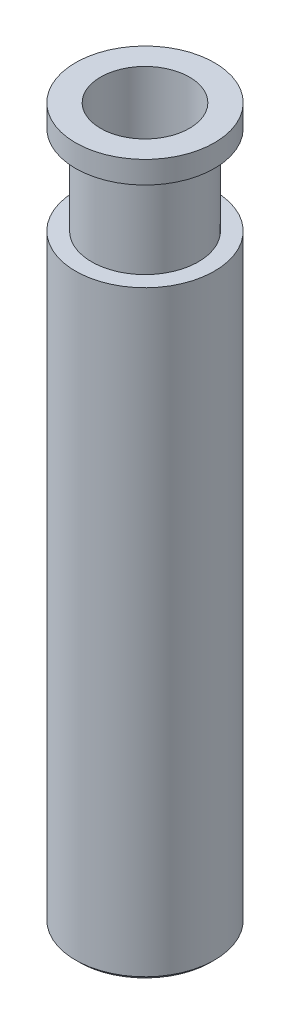
SolidWorks part; units mm, degrees
ref_plane "Front Plane" through (0, 0, 0) normal (0, 0, 1) x (1, 0, 0)
ref_plane "Top Plane" through (0, 0, 0) normal (0, 1, 0) x (1, 0, 0)
ref_plane "Right Plane" through (0, 0, 0) normal (1, 0, 0) x (0, 0, -1)
sketch "Sketch1" plane through (0, 0, 0) normal (0, 1, 0) x (1, 0, 0)
  circle A0 centre (0, 0) radius 4.9594
extrude "Boss-Extrude1" add sketch "Sketch1" against normal blind 1.5875
sketch "Sketch2" plane through (0, -1.5875, 0) normal (0, -1, 0) x (1, 0, 0)
  circle A0 centre (0, 0) radius 3.81
extrude "Boss-Extrude2" add sketch "Sketch2" along normal blind 6.35
sketch "Sketch3" plane through (0, -7.9375, 0) normal (0, -1, 0) x (1, 0, 0)
  circle A0 centre (0, 0) radius 4.9594
extrude "Boss-Extrude4" add sketch "Sketch3" along normal blind 42.8625
chamfer "Chamfer1" distance 0.254 angle 45 1 edges at (0, -50.8, -4.9594)
sketch "Sketch4" plane through (0, 0, 0) normal (0, 1, 0) x (1, 0, 0)
  circle A0 centre (0, 0) radius 3.175
extrude "Cut-Extrude1" cut sketch "Sketch4" against normal blind 7.9375
